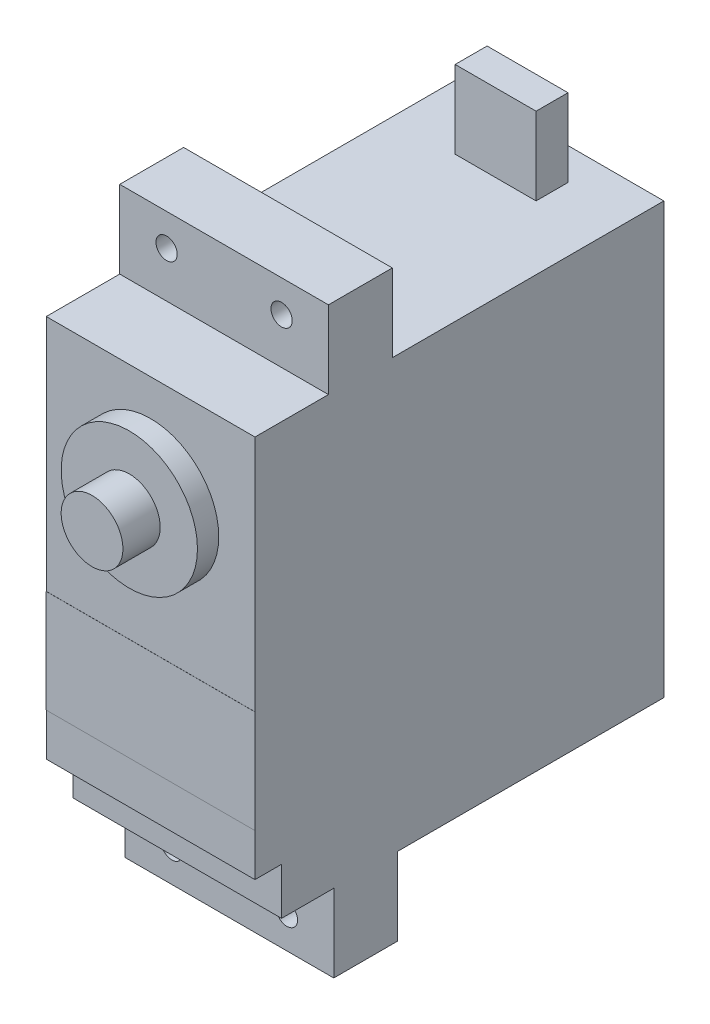
SolidWorks part; units mm, degrees
ref_plane "正面" through (0, 0, 0) normal (0, 0, 1) x (1, 0, 0)
ref_plane "平面" through (0, 0, 0) normal (0, 1, 0) x (1, 0, 0)
ref_plane "右側面" through (0, 0, 0) normal (1, 0, 0) x (0, 0, -1)
sketch "ｽｹｯﾁ2" plane through (0, 0, 0) normal (0, 0, 1) x (1, 0, 0)
  line L1 (15.8646, 20.4232) -> (35.4646, 20.4232)
  line L2 (15.8646, 20.4232) -> (15.8646, -19.9768)
  line L3 (15.8646, -19.9768) -> (35.4646, -19.9768)
  line L4 (35.4646, 20.4232) -> (35.4646, -19.9768)
  dimension "D1" = 40.4
  dimension "D2" = 19.6
extrude "ﾎﾞｽ - 押し出し2" add sketch "ｽｹｯﾁ2" along normal blind 35.9
sketch "ｽｹｯﾁ8" plane through (0, 0, 35.9) normal (0, 0, 1) x (1, 0, 0)
  line L0 (35.4646, -19.9768) -> (35.4646, 20.4232) construction
  line L1 (15.8646, 20.4232) -> (35.4646, 20.4232)
  line L2 (15.8646, 20.4232) -> (15.8646, -15.5768)
  line L3 (15.8646, -15.5768) -> (35.4646, -15.5768)
  line L4 (35.4646, 20.4232) -> (35.4646, -15.5768)
  dimension "D1" = 36
extrude "ﾎﾞｽ - 押し出し4" add sketch "ｽｹｯﾁ8" along normal blind 2.5
sketch "ｽｹｯﾁ9" plane through (0, 20.4232, 0) normal (0, 1, 0) x (1, 0, 0)
  line L0 (25.6646, 0) -> (25.6646, -25.5)
  line L1 (35.4646, 0) -> (15.8646, 0) construction
  line L2 (35.4646, -38.4) -> (35.4646, 0) construction
  line L3 (35.4646, -25.4998) -> (15.8646, -25.4998)
  line L4 (35.4646, -25.4998) -> (35.4646, -31.4998)
  line L5 (35.4646, -31.4998) -> (15.8646, -31.4998)
  line L6 (15.8646, -25.4998) -> (15.8646, -31.4998)
  line L7 (15.8646, -38.4) -> (15.8646, 0) construction
  dimension "D1" = 25.5
  dimension "D2" = 6
extrude "ﾎﾞｽ - 押し出し5" add sketch "ｽｹｯﾁ9" along normal blind 7.3
sketch "ｽｹｯﾁ10" plane through (0, -19.9768, 0) normal (0, -1, 0) x (1, 0, 0)
  line L0 (25.6646, 0) -> (25.6646, 25)
  line L1 (15.8646, 0) -> (35.4646, 0) construction
  line L2 (15.8646, 35.9) -> (15.8646, 0) construction
  line L3 (15.8646, 25) -> (35.4646, 25)
  line L4 (15.8646, 25) -> (15.8646, 31)
  line L5 (15.8646, 31) -> (35.4646, 31)
  line L6 (35.4646, 25) -> (35.4646, 31)
  line L7 (35.4646, 35.9) -> (35.4646, 0) construction
  line M4 (35.4646, 0) -> (35.4646, 35.9)
  line M6 (15.8646, 35.9) -> (15.8646, 0)
  dimension "D1" = 25
  dimension "D2" = 6
extrude "ﾎﾞｽ - 押し出し6" add sketch "ｽｹｯﾁ10" along normal blind 7.3 contours L5 L3 M6 M4
sketch "ｽｹｯﾁ11" plane through (0, 20.4232, 0) normal (0, 1, 0) x (1, 0, 0)
  line L0 (25.6646, 0) -> (25.6646, -3)
  line L1 (35.4646, 0) -> (15.8646, 0) construction
  line L2 (25.6646, -3) -> (21.8646, -3)
  line L4 (21.8646, -3) -> (29.4646, -3)
  line L5 (21.8646, -3) -> (21.8646, -6)
  line L6 (21.8646, -6) -> (29.4646, -6)
  line L7 (29.4646, -3) -> (29.4646, -6)
  dimension "D1" = 3
  dimension "D2" = 3.8
  dimension "D3" = 3
  dimension "D4" = 7.6
extrude "ﾎﾞｽ - 押し出し7" add sketch "ｽｹｯﾁ11" along normal blind 7.3 contours L7 L4 L2 L5 L6
sketch "ｽｹｯﾁ12" plane through (0, 0, 38.4) normal (0, 0, 1) x (1, 0, 0)
  line L0 (25.6646, 20.4232) -> (25.6646, 10.6232)
  line L1 (35.4646, 20.4232) -> (15.8646, 20.4232) construction
  circle A0 centre (25.6646, 10.6232) radius 9.8
  dimension "D1" = 9.8
sketch "ｽｹｯﾁ13" plane through (0, 0, 38.4) normal (0, 0, 1) x (1, 0, 0)
  circle A0 centre (25.6646, 10.6232) radius 6.4
extrude "ﾎﾞｽ - 押し出し8" add sketch "ｽｹｯﾁ13" along normal blind 2
sketch "ｽｹｯﾁ15" plane through (0, 0, 40.4) normal (0, 0, 1) x (1, 0, 0)
  circle A0 centre (25.6646, 10.6232) radius 2.9
extrude "ﾎﾞｽ - 押し出し9" add sketch "ｽｹｯﾁ15" along normal blind 3.5
sketch "ｽｹｯﾁ16" plane through (0, 0, 38.4) normal (0, 0, 1) x (1, 0, 0)
  line L0 (15.8646, -15.5768) -> (15.8646, -11.5768)
  line L1 (15.8646, 20.4232) -> (15.8646, -15.5768) construction
  line L2 (35.4646, -15.5768) -> (35.4646, 20.4232) construction
  line L3 (15.8646, -11.5768) -> (35.4646, -11.5768)
  line L4 (15.8646, -11.5768) -> (15.8646, -1.9268)
  line L5 (15.8646, -1.9268) -> (35.4646, -1.9268)
  line L6 (35.4646, -11.5768) -> (35.4646, -1.9268)
  dimension "D1" = 4
  dimension "D2" = 9.65
extrude "ﾎﾞｽ - 押し出し10" add sketch "ｽｹｯﾁ16" along normal blind 0.01 contours L3 L6 L5 L4
sketch "ｽｹｯﾁ17" plane through (0, 0, 31.4998) normal (0, 0, 1) x (1, 0, 0)
  line L0 (25.6646, 27.7232) -> (31.0646, 27.7232)
  line L1 (35.4646, 27.7232) -> (15.8646, 27.7232) construction
  line L2 (35.4646, 20.4232) -> (15.8646, 20.4232) construction
  circle A0 centre (31.0646, 24.7232) radius 1
  dimension "D2" = 4.3
  dimension "D1" = 5.4
extrude "ｶｯﾄ - 押し出し1" cut sketch "ｽｹｯﾁ17" against normal blind 10 contours A0
sketch "ｽｹｯﾁ18" plane through (0, 0, 31.4998) normal (0, 0, 1) x (1, 0, 0)
  line L1 (15.8646, 27.7232) -> (20.2646, 27.7232)
  line L2 (15.8646, 27.7232) -> (15.8646, 24.7232)
  line L3 (15.8646, 24.7232) -> (20.2646, 24.7232)
  line L4 (20.2646, 27.7232) -> (20.2646, 24.7232)
  circle A0 centre (20.2646, 24.7232) radius 1
  dimension "D1" = 3
  dimension "D2" = 4.4
extrude "ｶｯﾄ - 押し出し2" cut sketch "ｽｹｯﾁ18" against normal blind 10 contours L3 A0 L4 | L4 A0 L3
sketch "ｽｹｯﾁ19" plane through (0, 0, 31) normal (0, 0, 1) x (1, 0, 0)
  line L0 (15.8646, -27.2768) -> (35.4646, -27.2768) construction
  line L1 (15.8646, -27.2768) -> (15.8646, -19.9768) construction
  circle A0 centre (20.2646, -24.2768) radius 1
  circle A1 centre (31.0646, -24.2768) radius 1
  point P8 (0, 0)
  dimension "D1" = 3
  dimension "D2" = 4.4
  dimension "D3" = 10.8
extrude "ｶｯﾄ - 押し出し3" cut sketch "ｽｹｯﾁ19" against normal blind 10
